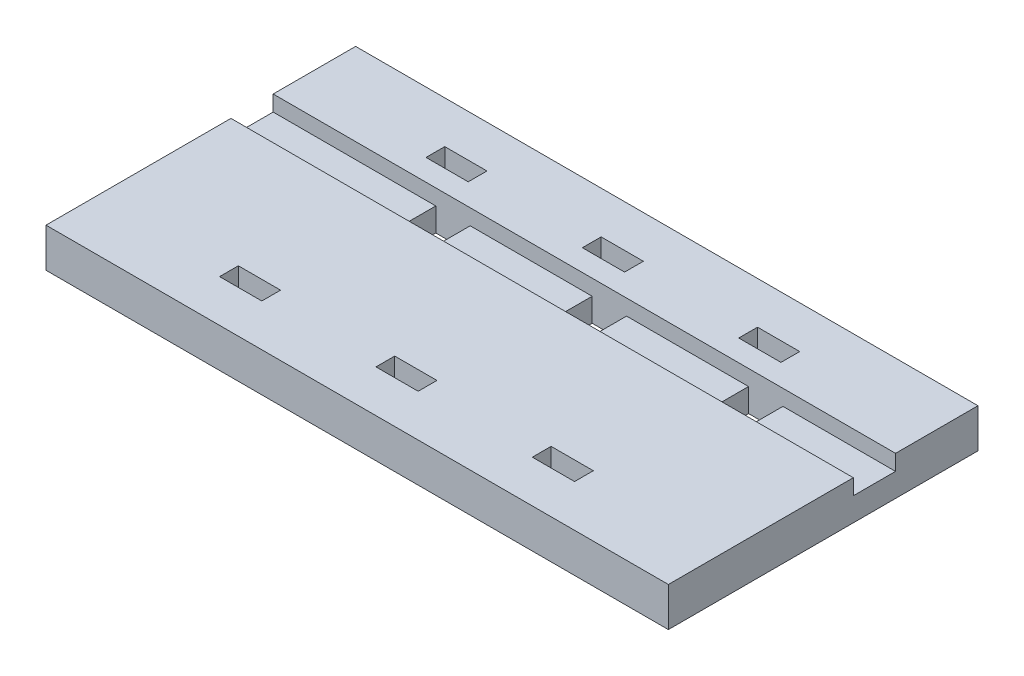
SolidWorks part; units mm, degrees
material "POLYURETHANE (11671)"
ref_plane "Front Plane" through (0, 0, 0) normal (0, 0, 1) x (1, 0, 0)
ref_plane "Top Plane" through (0, 0, 0) normal (0, 1, 0) x (1, 0, 0)
ref_plane "Right Plane" through (0, 0, 0) normal (1, 0, 0) x (0, 0, -1)
sketch "Sketch1" plane through (0, 0, 0) normal (0, 1, 0) x (1, 0, 0)
  line L1 (-50.546, -25.146) -> (50.546, -25.146)
  line L2 (-50.546, -25.146) -> (-50.546, 25.146)
  line L3 (-50.546, 25.146) -> (50.546, 25.146)
  line L4 (50.546, -25.146) -> (50.546, 25.146)
  line L5 (0, 25.146) -> (0, -25.146) construction
  line L6 (-50.546, 0) -> (50.546, 0) construction
  point P0 (0, 0)
  dimension "D1" = 50.292
  dimension "D2" = 101.092
extrude "Boss-Extrude1" add sketch "Sketch1" along normal blind 6.35
sketch "Sketch2" plane through (0, 6.35, 0) normal (0, 1, 0) x (1, 0, 0)
  line L0 (1.27, 4.8935) -> (6.858, 4.8935)
  line L1 (1.27, 4.8935) -> (1.27, 11.7515)
  line L2 (6.858, 4.8935) -> (6.858, 11.7515)
  line L3 (1.27, 11.7515) -> (6.858, 11.7515)
  circle A0 centre (4.064, 0) radius 5.635 construction
  dimension "D1" = 11.27
  dimension "D2" = 4.064
  dimension "D3" = 5.588
  dimension "D4" = 6.858
extrude "Wire Hole" cut sketch "Sketch2" against normal through all contours L3 L1 L0 L2
sketch "Sketch3" plane through (0, 6.35, 0) normal (0, 1, 0) x (1, 0, 0)
  line L0 (-3.81, 15.24) -> (3.048, 15.24)
  line L1 (-3.81, 15.24) -> (-3.81, 18.288)
  line L2 (3.048, 15.24) -> (3.048, 18.288)
  line L3 (-3.81, 18.288) -> (3.048, 18.288)
  line L4 (-2.794, 0) -> (2.794, 0) construction
  dimension "D1" = 3.048
  dimension "D2" = 6.858
  dimension "D3" = 3.048
  dimension "D4" = 15.24
extrude "Cut-Extrude2" cut sketch "Sketch3" against normal blind 3.81
mirror "Mirror1" about plane through (0, 0, 0) normal (0, 0, 1) of "Cut-Extrude2"
pattern_linear "LPattern1" count 2 spacing 25.4 along (-1, 0, 0) count 2 spacing 25.4 along (1, 0, 0) of "Wire Hole", "Cut-Extrude2", "Mirror1"
sketch "Sketch4" plane through (0, 6.35, 0) normal (0, 1, 0) x (1, 0, 0)
  line L0 (-50.546, 25.146) -> (-50.546, -25.146) construction
  line L1 (-50.546, 11.7515) -> (50.546, 11.7515)
  line L2 (-50.546, 11.7515) -> (-50.546, 4.8935)
  line L3 (-50.546, 4.8935) -> (50.546, 4.8935)
  line L4 (50.546, 11.7515) -> (50.546, 4.8935)
  line L5 (50.546, -25.146) -> (50.546, 25.146) construction
  line L7 (1.27, 11.7515) -> (6.858, 11.7515) construction
  line L8 (1.27, 4.8935) -> (6.858, 4.8935) construction
extrude "Cut-Extrude3" cut sketch "Sketch4" against normal blind 2.54
equation "\"Arrow Height\"= 1in"
equation "\"Button Height\"= 2in"
equation "\"Button Width\"= 4in"
equation "\"Haptic Diameter\"= 10mm"
equation "\"Haptic Thickness\"= 2.7mm"
equation "\"D1@Sketch1\"=\"Button Height\"-\"Tolerance\""
equation "\"D2@Sketch1\"=\"Button Width\"-\"Tolerance\""
equation "\"Arrow Spacing\"= 1in"
equation "\"Arrow Width\"= 0.75in"
equation "\"Haptic Wire Angle\"= 63.43"
equation "\"Haptic Wire Width\"= .2in"
equation "\"Hatic Wire Height\"= .25in"
equation "\"D1@Sketch2\"=\"Haptic Diameter\"+.05"
equation "\"D3@Sketch2\"=\"Haptic Wire Width\"+.02"
equation "\"D4@Sketch2\"=\"Hatic Wire Height\"+.02"
equation "\"Tolerance\"= .02in"
